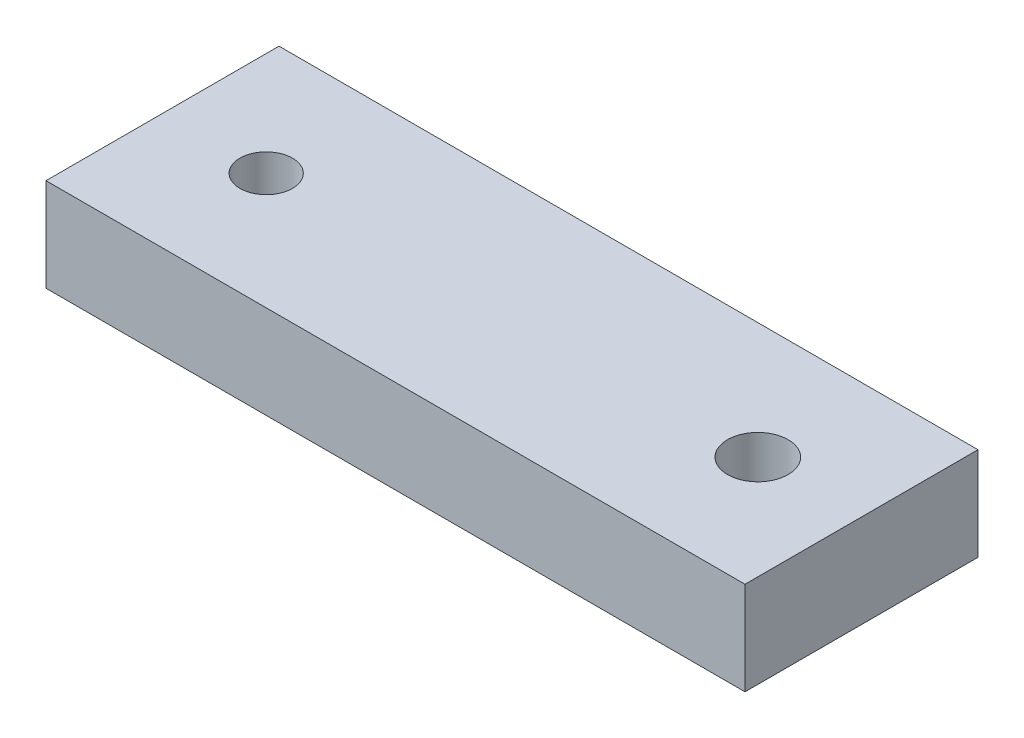
SolidWorks part; units mm, degrees
ref_plane "前视基准面" through (0, 0, 0) normal (0, 0, 1) x (1, 0, 0)
ref_plane "上视基准面" through (0, 0, 0) normal (0, 1, 0) x (1, 0, 0)
ref_plane "右视基准面" through (0, 0, 0) normal (1, 0, 0) x (0, 0, -1)
sketch "草图1" plane through (0, 0, 0) normal (0, 1, 0) x (1, 0, 0)
  line L1 (-34.8294, 5.748) -> (25.1706, 5.748)
  line L2 (-34.8294, 5.748) -> (-34.8294, -14.252)
  line L3 (-34.8294, -14.252) -> (25.1706, -14.252)
  line L4 (25.1706, 5.748) -> (25.1706, -14.252)
  dimension "D1" = 60
  dimension "D2" = 20
extrude "凸台-拉伸1" add sketch "草图1" along normal blind 8
sketch "草图2" plane through (0, 8, 0) normal (0, 1, 0) x (1, 0, 0)
  circle A0 centre (-25.9294, -4.252) radius 2.2545
  circle A1 centre (16.2706, -4.252) radius 2.6
  dimension "D3" = 4.509
  dimension "D4" = 5.2
extrude "切除-拉伸1" cut sketch "草图2" against normal through all
